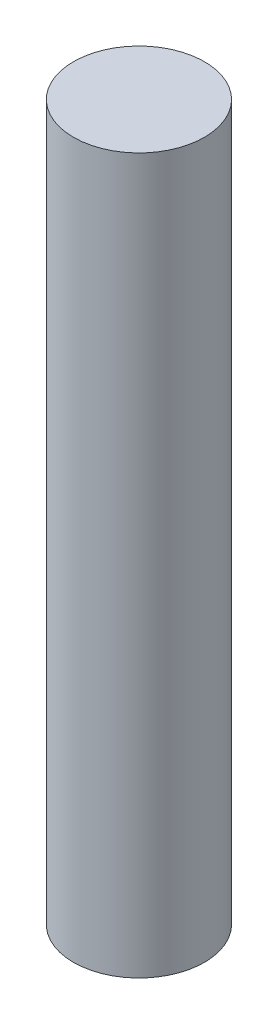
SolidWorks part; units mm, degrees
ref_plane "Front Plane" through (0, 0, 0) normal (0, 0, 1) x (1, 0, 0)
ref_plane "Top Plane" through (0, 0, 0) normal (0, 1, 0) x (1, 0, 0)
ref_plane "Right Plane" through (0, 0, 0) normal (1, 0, 0) x (0, 0, -1)
sketch "Sketch1" plane through (0, 0, 0) normal (0, 1, 0) x (1, 0, 0)
  circle A0 centre (0, 0) radius 5.5
extrude "Boss-Extrude1" add sketch "Sketch1" along normal blind 60
